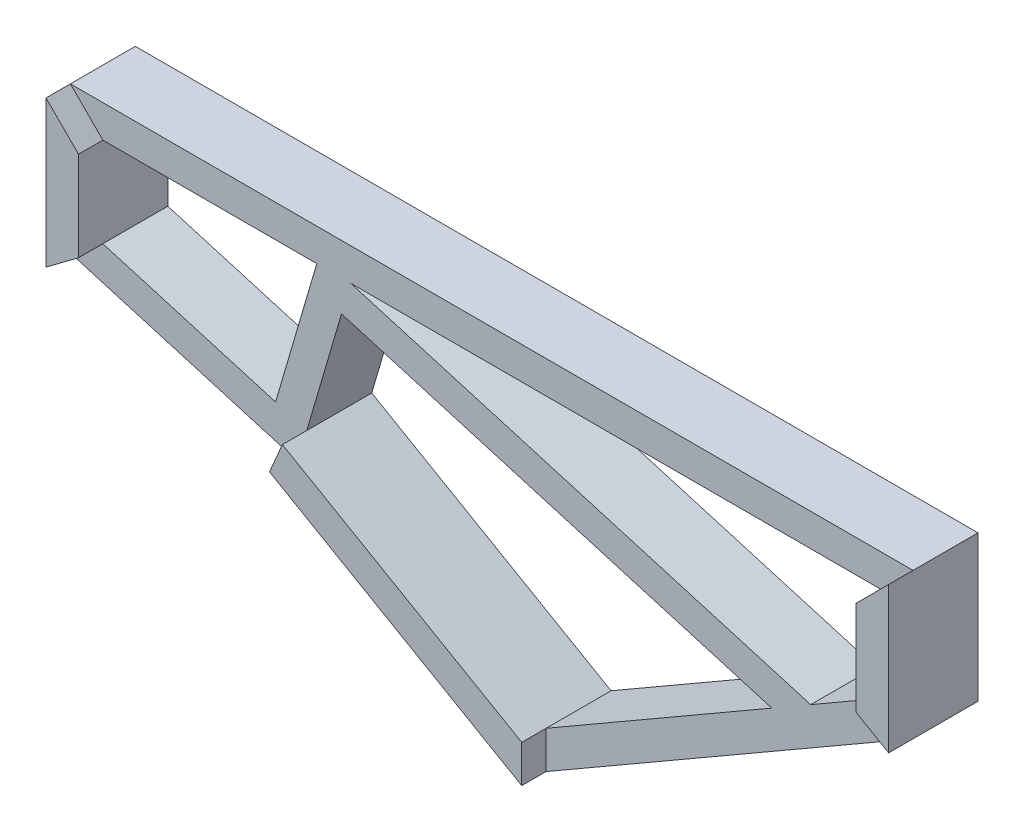
SolidWorks part; units mm, degrees
ref_plane "Спереди" through (0, 0, 0) normal (0, 0, 1) x (1, 0, 0)
ref_plane "Сверху" through (0, 0, 0) normal (0, 1, 0) x (1, 0, 0)
ref_plane "Справа" through (0, 0, 0) normal (1, 0, 0) x (0, 0, -1)
sketch "Эскиз6" plane through (0, 0, 0) normal (1, 0, 0) x (0, 0, -1)
  line L1 (-38.5518, -19.2165) -> (37.4482, -19.2165)
  line L2 (-38.5518, -19.2165) -> (-38.5518, 16.7835)
  line L3 (-38.5518, 16.7835) -> (37.4482, 16.7835)
  line L4 (37.4482, -19.2165) -> (37.4482, 16.7835)
  line L5 (-40.5518, 18.7835) -> (39.4482, 18.7835)
  line L6 (-40.5518, 18.7835) -> (-40.5518, -21.2165)
  line L7 (-40.5518, -21.2165) -> (39.4482, -21.2165)
  line L8 (39.4482, 18.7835) -> (39.4482, -21.2165)
  dimension "D1" = 36
  dimension "D2" = 76
  dimension "D3" = 2
  dimension "D4" = 2
  dimension "D5" = 2
  dimension "D6" = 2
sketch3d "Трехмерный эскиз5"
  line L0 (0, 0, 0) -> (1000, 0, 0)
  line L1 (1000, 0, 0) -> (1000, -150, 0)
  line L2 (1000, -150, 0) -> (566.9873, -400, 0)
  line L3 (566.9873, -400, 0) -> (263.8784, -225, 0)
  line L4 (263.8784, -225, 0) -> (0, -147.5843, 0)
  line L5 (0, -147.5843, 0) -> (0, 0, 0)
  line L6 (263.8784, -225, 0) -> (393.7822, 0, 0)
  line L7 (393.7822, 0, 0) -> (826.7949, -250, 0)
  dimension "D1" = 1000
  dimension "D2" = 150
  dimension "D4" = 400
  dimension "D5" = 225
  dimension "D6" = 350
  dimension "D7" = 275
  dimension "D8" = 500
sweep "По траектории13" add profiles "Эскиз6" path "Трехмерный эскиз5"
sketch "Эскиз14" plane through (-33.8938, -115.53, 0) normal (0.2815, 0.9596, 0) x (0.9596, -0.2815, 0)
  line L0 (319.0859, 39.4482) -> (57.433, 39.4482) construction
  line L1 (319.0859, -40.5518) -> (279.0859, -40.5518)
  line L2 (319.0859, -40.5518) -> (319.0859, 39.4482)
  line L3 (319.0859, 39.4482) -> (279.0859, 39.4482)
  line L4 (279.0859, -40.5518) -> (279.0859, 39.4482)
  point P7 (279.0859, -0.5518)
  dimension "D1" = 40
extrude "Бобышка-Вытянуть1" add sketch "Эскиз14" along normal blind 194
sketch "Эскиз15" plane through (306.1814, -89.8264, 0) normal (0.9596, -0.2815, 0) x (0, 0, -1)
  line L0 (-40.5518, 71.5015) -> (-40.5518, -120.3992) construction
  line L1 (-40.5518, 71.5014) -> (39.4482, 71.5014)
  line L2 (-40.5518, 71.5014) -> (-40.5518, 31.5014)
  line L3 (-40.5518, 31.5014) -> (39.4482, 31.5014)
  line L4 (39.4482, 71.5014) -> (39.4482, 31.5014)
  line L5 (39.4482, 71.5015) -> (39.4482, -120.3992) construction
  line L6 (-40.5518, 71.5015) -> (39.4482, 71.5015) construction
  dimension "D1" = 40
  dimension "D2" = 0.0001
extrude "Бобышка-Вытянуть2" add sketch "Эскиз15" along normal blind 595
sketch "Эскиз17" plane through (0, 0, 40.5518) normal (0, 0, 1) x (1, 0, 0)
  line L0 (-18.7835, 18.7835) -> (21.2165, -21.2165)
  line L1 (21.2165, -21.2165) -> (21.2165, -131.698)
  line L2 (21.2165, -131.698) -> (21.2165, -21.2165) construction
  line L3 (21.2165, -131.698) -> (-18.7835, -161.6489)
  line L4 (-18.7835, -161.6489) -> (-18.7835, 18.7835)
extrude "Бобышка-Вытянуть3" add sketch "Эскиз17" along normal blind 30
sketch "Эскиз18" plane through (0, 0, 40.5518) normal (0, 0, 1) x (1, 0, 0)
  line L0 (272.2876, -205.3564) -> (256.4335, -242.391)
  line L1 (256.4335, -242.391) -> (566.9873, -421.6893)
  line L2 (566.9873, -421.6893) -> (566.9873, -375.5013)
  line L3 (566.9873, -375.5013) -> (272.2876, -205.3564)
extrude "Бобышка-Вытянуть4" add sketch "Эскиз18" along normal blind 30
sketch "Эскиз19" plane through (0, 0, 40.5518) normal (0, 0, 1) x (1, 0, 0)
  line L0 (1018.7835, 18.7835) -> (978.7835, -21.2165)
  line L1 (978.7835, -21.2165) -> (978.7835, -137.7506)
  line L2 (978.7835, -137.7506) -> (1018.7835, -160.8447)
  line L3 (1018.7835, -160.8447) -> (1018.7835, 18.7835)
extrude "Бобышка-Вытянуть5" add sketch "Эскиз19" along normal blind 30
